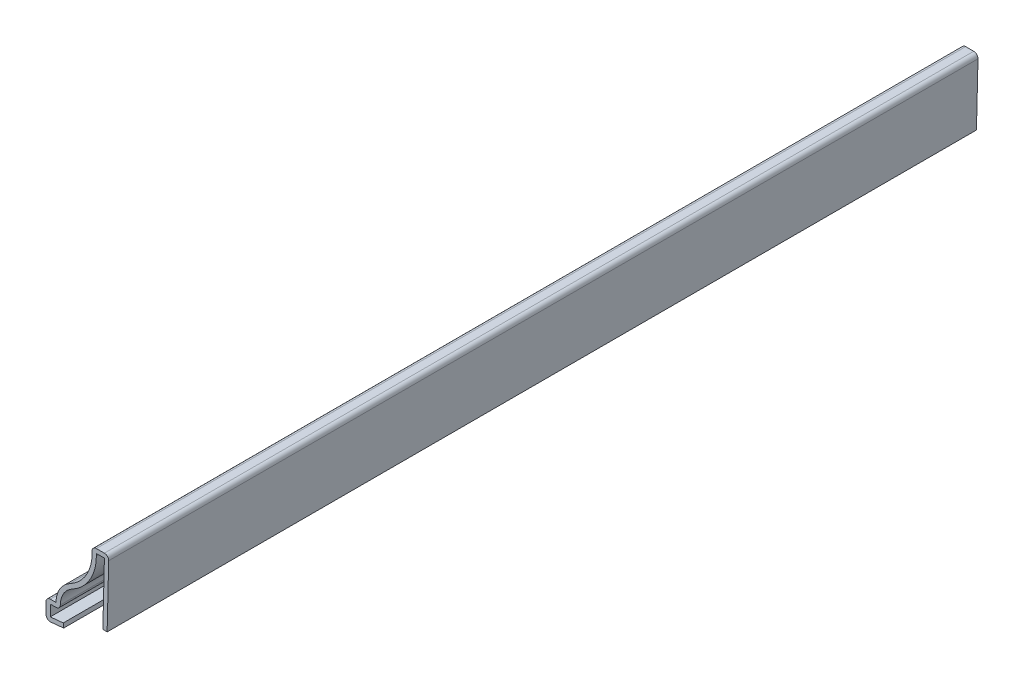
SolidWorks part; units mm, degrees
ref_plane "Front Plane" through (0, 0, 0) normal (0, 0, 1) x (1, 0, 0)
ref_plane "Top Plane" through (0, 0, 0) normal (0, 1, 0) x (1, 0, 0)
ref_plane "Right Plane" through (0, 0, 0) normal (1, 0, 0) x (0, 0, -1)
sketch "Sketch2" plane through (0, 0, 0) normal (0, 0, 1) x (1, 0, 0)
  line L0 (0, 0) -> (-14.9066, 0) construction
  line L1 (0, 20.6375) -> (-0.3969, 4.7625)
  line L3 (0, 20.6375) -> (-3.9688, 20.6375)
  line L4 (-12.5253, 4.7625) -> (-14.9066, 4.7625)
  line L5 (-14.9066, 4.7625) -> (-14.9066, 0)
  line L6 (-14.9066, 0) -> (-10.7156, 0.3969)
  line L7 (-3.9688, 20.6375) -> (-3.9688, 19.05)
  arc A0 (-3.9688, 19.05) -> (-9.1862, 10.3143) centre (-13.8906, 19.05) cw
  arc A1 (-9.1862, 10.3143) -> (-12.5253, 4.7625) centre (-6.1754, 4.7235) ccw
  point P4 (0, 0)
  point P13 (-15.0549, 4.7625)
  dimension "D4" = 9.9219
  dimension "D6" = 6.35
  dimension "D2" = 20.6375
  dimension "D3" = 4.7625
  dimension "D5" = 1.5875
  dimension "D7" = 3.9688
  dimension "D8" = 0.3969
  dimension "D9" = 2.3813
  dimension "D10" = 4.191
  dimension "D11" = 0.7937
  dimension "D12" = 15.875
  dimension "D13" = 14.9066
extrude "Extrude-Thin1" add sketch "Sketch2" against normal blind 206.375 thin
fillet "Fillet1" radius 1.016 5 edges at (-14.9066, 0, -103.1875) (-14.9066, 4.7625, -103.1875) (-11.4191, 3.7465, -103.1875) (-3.9688, 20.6375, -103.1875) (0, 20.6375, -103.1875)
